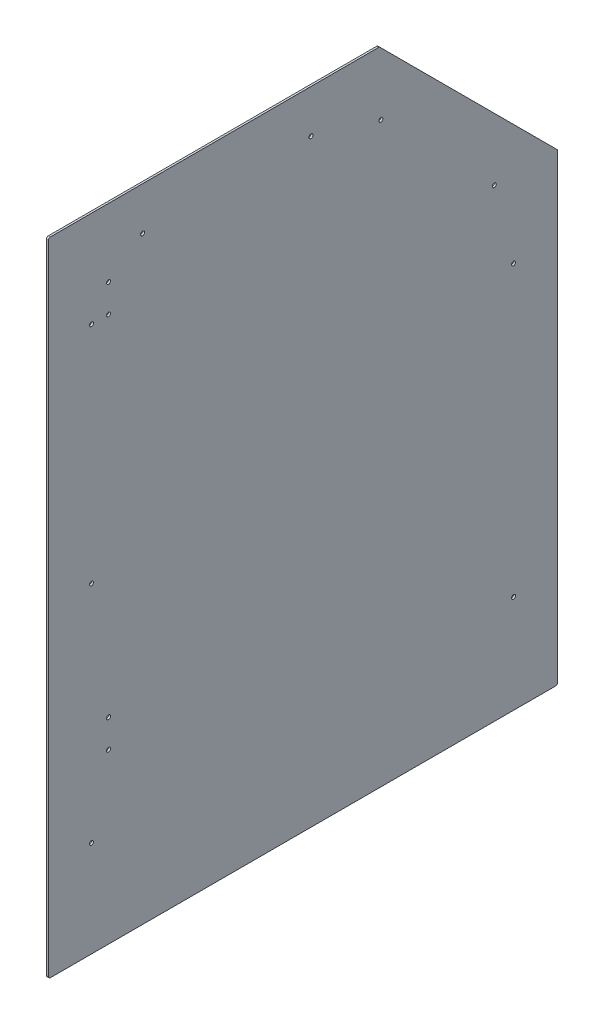
SolidWorks part; units mm, degrees
material "PC High Viscosity"
ref_plane "Front Plane" through (0, 0, 0) normal (0, 0, 1) x (1, 0, 0)
ref_plane "Top Plane" through (0, 0, 0) normal (0, 1, 0) x (1, 0, 0)
ref_plane "Right Plane" through (0, 0, 0) normal (1, 0, 0) x (0, 0, -1)
sketch "Sketch1" plane through (0, 0, 0) normal (1, 0, 0) x (0, 0, -1)
  line L0 (0, 0) -> (0, 1016)
  line L1 (0, 1016) -> (524.2328, 1016)
  line L2 (524.2328, 1016) -> (806.45, 733.7828)
  line L3 (806.45, 733.7828) -> (806.45, 0)
  line L4 (806.45, 0) -> (0, 0)
  line L5 (0, 889) -> (0, 127) construction
  line L6 (742.95, 647.7) -> (742.95, 368.3) construction
  line L7 (742.95, 63.5) -> (63.5, 63.5) construction
  line L8 (63.5, 63.5) -> (63.5, 952.5) construction
  line L9 (63.5, 952.5) -> (488.95, 952.5) construction
  line L10 (488.95, 952.5) -> (742.95, 698.5) construction
  line L11 (742.95, 698.5) -> (742.95, 63.5) construction
  point P8 (0, 508)
  point P9 (0, 508)
  point P10 (742.95, 508)
  dimension "D1" = 1016
  dimension "D2" = 762
  dimension "D3" = 279.4
  dimension "D4" = 50.8
  dimension "D5" = 742.95
  dimension "D7" = 45
  dimension "D6" = 63.5
  dimension "D8" = 63.5
  dimension "D9" = 63.5
  dimension "D10" = 63.5
  dimension "D11" = 69.85
extrude "Boss-Extrude1" add sketch "Sketch1" along normal blind 3.175
sketch "Sketch2" plane through (3.175, 0, 0) normal (1, 0, 0) x (0, 0, -1)
  line L1 (0, 0) -> (152.4, 0)
  line L2 (0, 0) -> (0, 76.2)
  line L3 (0, 76.2) -> (152.4, 76.2)
  line L4 (152.4, 0) -> (152.4, 76.2)
  line L5 (806.45, 0) -> (654.05, 0)
  line L6 (806.45, 0) -> (806.45, 76.2)
  line L7 (806.45, 76.2) -> (654.05, 76.2)
  line L8 (654.05, 0) -> (654.05, 76.2)
  dimension "D1" = 76.2
  dimension "D3" = 152.4
extrude "Cut-Extrude1" [suppressed] cut sketch "Sketch2" against normal through all
hole_wizard "1/4 (0.25) Diameter Hole1" positions "Sketch3" profile "Sketch4" hole size "1/4" standard "ANSI Inch" end condition through all
sketch "Sketch3" plane through (3.175, 0, 0) normal (1, 0, 0) x (0, 0, -1)
  line L27 (63.5, 952.5) -> (63.5, 63.5)
  line L30 (63.5, 63.5) -> (742.95, 63.5)
  line L33 (742.95, 63.5) -> (742.95, 707.4803)
  line L34 (742.95, 707.4803) -> (497.9303, 952.5)
  line L35 (497.9303, 952.5) -> (63.5, 952.5)
  line L36 (63.5, 952.5) -> (63.5, 63.5) construction
  line L39 (63.5, 57.15) -> (438.15, 57.15) construction
  line L42 (742.95, 63.5) -> (742.95, 707.4803) construction
  line L43 (742.95, 707.4803) -> (497.9303, 952.5) construction
  line L44 (497.9303, 952.5) -> (63.5, 952.5) construction
  line L45 (68.2625, 0) -> (68.2625, 1016) construction
  line L46 (524.2328, 1016) -> (0, 1016) construction
  line L48 (0, 0) -> (806.45, 0) construction
  line L49 (0, 1016) -> (0, 0) construction
  line L50 (710.6211, 739.8092) -> (706.1309, 735.3191) construction
  line L52 (706.1309, 735.3191) -> (526.5258, 914.9242) construction
  line L53 (403.225, 0) -> (403.225, 1016) construction
  line L54 (95.25, 266.7) -> (95.25, 311.15) construction
  line L55 (0, 1016) -> (0, 0) construction
  line L56 (0, 0) -> (806.45, 0) construction
  point P82 (68.2625, 152.4)
  point P84 (68.2625, 508)
  point P86 (68.2625, 863.6)
  point P99 (149.225, 947.7375)
  point P101 (415.925, 947.7375)
  point P110 (736.6, 155.575)
  point P112 (736.6, 612.775)
  point P119 (706.1309, 735.3191)
  point P121 (526.5258, 914.9242)
  point P253 (95.25, 266.7)
  point P255 (95.25, 311.15)
  point P268 (95.25, 863.6)
  point P269 (95.25, 908.05)
  point P270 (95.25, 766.9793)
  dimension "D2" = 355.6
  dimension "D3" = 355.6
  dimension "D4" = 4.7625
  dimension "D5" = 266.7
  dimension "D6" = 149.225
  dimension "D7" = 4.7625
  dimension "D8" = 155.575
  dimension "D9" = 457.2
  dimension "D10" = 6.35
  dimension "D11" = 6.35
  dimension "D12" = 45.72
  dimension "D13" = 254
  dimension "D16" = 57.15
  dimension "D14" = 44.45
  dimension "D15" = 95.25
  dimension "D17" = 266.7
  dimension "D19" = 863.6
  dimension "D1" = 63.5
  dimension "D18" = 2
sketch "Sketch4" plane through (3.175, 908.05, -95.25) normal (0, 1, 0) x (0, 0, -1)
  line L0 (0, 0) -> (0, 3.175)
  line L1 (0, 3.175) -> (3.175, 3.175)
  line L2 (3.175, 3.175) -> (3.175, 0)
  line L5 (3.175, 0) -> (0, 0)
  line L11 (0, -6.35) -> (0, 107.95) construction
  dimension "Thru Hole Dia." = 6.35
  dimension "Thru Hole Depth" = 3.175
sketch "Sketch5" plane through (0, 0, 0) normal (-1, 0, 0) x (0, 0, 1)
  line L0 (-524.2328, 1016) -> (0, 1016) construction
  line L1 (0, 1016) -> (-76.2, 1016)
  line L2 (0, 1016) -> (0, 958.85)
  line L3 (0, 958.85) -> (-76.2, 958.85)
  line L4 (-76.2, 1016) -> (-76.2, 958.85)
  line L5 (-368.3, 1016) -> (-444.5, 1016)
  line L6 (-368.3, 1016) -> (-368.3, 958.85)
  line L7 (-368.3, 958.85) -> (-444.5, 958.85)
  line L8 (-444.5, 1016) -> (-444.5, 958.85)
  dimension "D1" = 76.2
  dimension "D2" = 292.1
  dimension "D3" = 57.15
extrude "Cut-Extrude2" [suppressed] cut sketch "Sketch5" against normal through all
fillet "Fillet1" radius 3.175 5 edges at (1.5875, 1016, 0) (1.5875, 1016, -524.2328) (1.5875, 733.7828, -806.45) (1.5875, 0, -806.45) (1.5875, 0, 0)
equation "\"D3@Sketch3\"=\"D2@Sketch3\""
equation "\"D7@Sketch3\"=\"D4@Sketch3\""
equation "\"D10@Sketch3\"=\"D11@Sketch3\""
